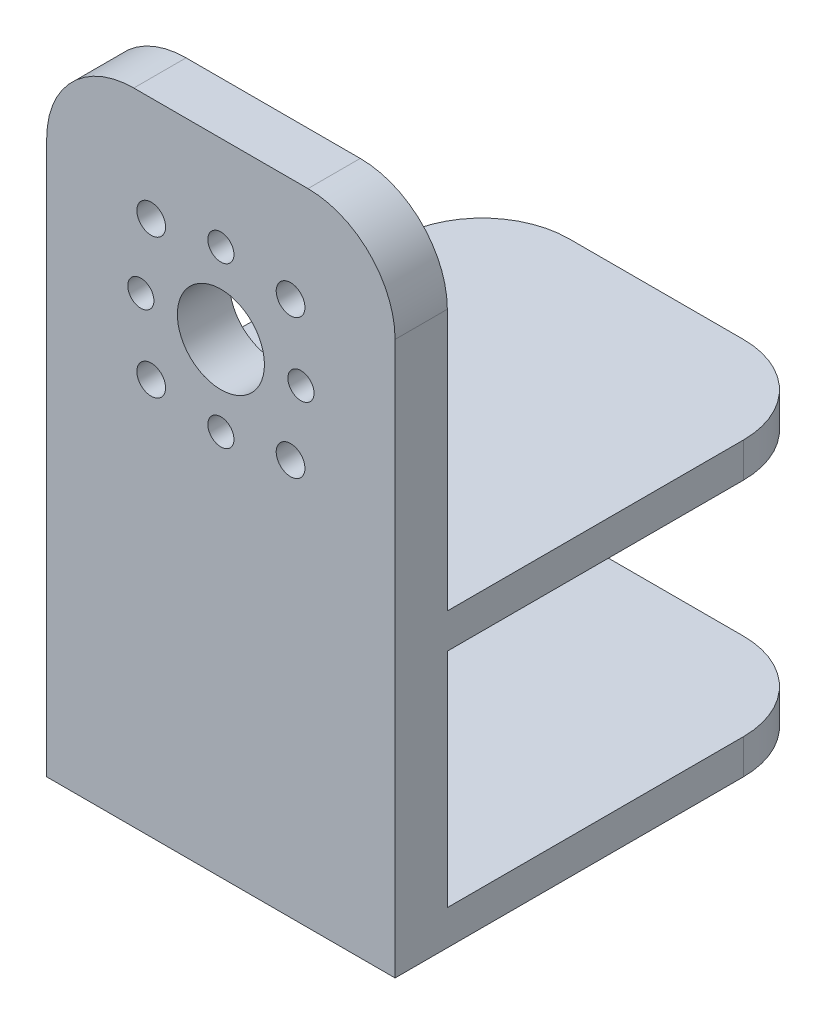
SolidWorks part; units mm, degrees
ref_plane "Front Plane" through (0, 0, 0) normal (0, 0, 1) x (1, 0, 0)
ref_plane "Top Plane" through (0, 0, 0) normal (0, 1, 0) x (1, 0, 0)
ref_plane "Right Plane" through (0, 0, 0) normal (1, 0, 0) x (0, 0, -1)
sketch "Sketch1" plane through (0, 0, 0) normal (0, 0, 1) x (1, 0, 0)
  line L1 (0, 0) -> (40, 0)
  line L2 (0, 0) -> (0, 40)
  line L3 (0, 40) -> (40, 40)
  line L4 (40, 0) -> (40, 40)
  circle A0 centre (20, 20) radius 5
  circle A9 centre (12, 28) radius 1.65
  circle A10 centre (20, 29.1924) radius 1.5
  circle A11 centre (29.1924, 20) radius 1.5
  circle A12 centre (20, 10.8076) radius 1.5
  circle A13 centre (10.8076, 20) radius 1.5
  circle A14 centre (28, 28) radius 1.65
  circle A15 centre (12, 12) radius 1.65
  circle A16 centre (28, 12) radius 1.65
  point P23 (37.1614, 47.3983)
  point P24 (21.5259, 47.3983)
  point P25 (21.8889, 34.3983)
  point P26 (0, 0)
  point P27 (0, 0)
  point P28 (0, 0)
  point P29 (0, 0)
  dimension "D3" = 10
  dimension "D10" = 3
  dimension "D13" = 8
  dimension "D15" = 3.3
  dimension "D1" = 40
  dimension "D2" = 40
  dimension "D4" = 20
  dimension "D5" = 20
  dimension "D6" = 13
  dimension "D7" = 13
  dimension "D8" = 13
  dimension "D9" = 45
  dimension "D11" = 16
  dimension "D12" = 16
  dimension "D14" = 8
extrude "Boss-Extrude1" add sketch "Sketch1" along normal blind 6
sketch "Sketch2" plane through (40, 0, 0) normal (1, 0, 0) x (0, 0, -1)
  line L0 (0, 0) -> (0, 40) construction
  line L1 (-6, 0) -> (44, 0)
  line L2 (-6, 0) -> (-6, -4)
  line L3 (-6, -4) -> (44, -4)
  line L4 (44, 0) -> (44, -4)
  line L5 (-6, -4) -> (0, -4)
  line L6 (-6, -4) -> (-6, -29.5)
  line L7 (-6, -29.5) -> (0, -29.5)
  line L8 (0, -4) -> (0, -29.5)
  line L9 (-6, -29.5) -> (44, -29.5)
  line L10 (-6, -29.5) -> (-6, -33.5)
  line L11 (-6, -33.5) -> (44, -33.5)
  line L12 (44, -29.5) -> (44, -33.5)
  dimension "D1" = 4
  dimension "D2" = 50
  dimension "D3" = 4
  dimension "D4" = 50
  dimension "D5" = 25.5
extrude "Boss-Extrude2" add sketch "Sketch2" against normal blind 40 contours L2 L1 L4 L3 | L6 L5 L8 L7 | L10 L9 L12 L11
sketch "Sketch3" plane through (0, 0, 0) normal (0, 0, -1) x (-1, 0, 0)
  circle A0 centre (-20, 29.1924) radius 3.5
  circle A1 centre (-20, 10.8076) radius 3.5
  circle A2 centre (-29.1924, 20) radius 3.5
  circle A3 centre (-10.8076, 20) radius 3.5
  dimension "D1" = 7
extrude "Cut-Extrude1" cut sketch "Sketch3" against normal blind 3
fillet "Fillet1" radius 10 6 edges at (40, -2, -44) (40, 40, 3) (0, 40, 3) (40, -31.5, -44) (0, -31.5, -44) (0, -2, -44)
